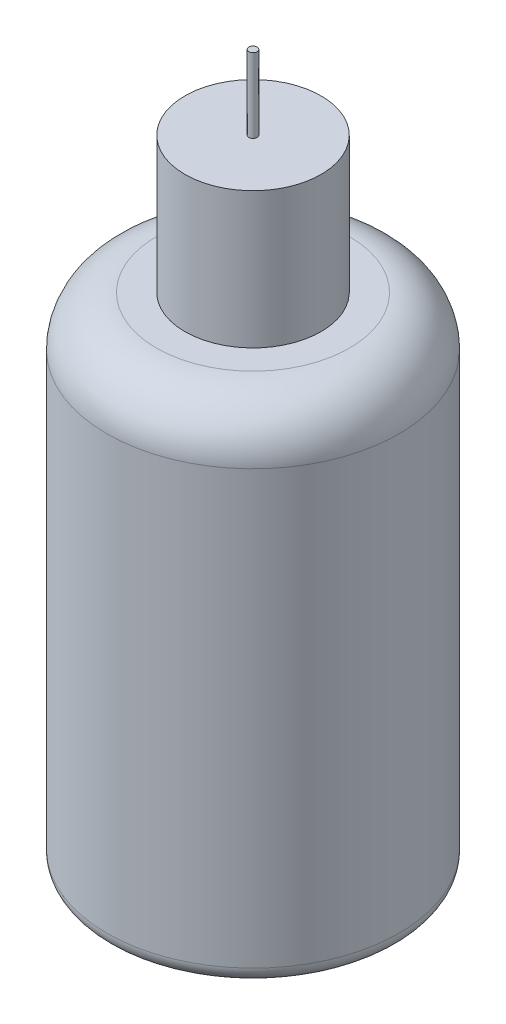
SolidWorks part; units mm, degrees
ref_plane "Alzado" through (0, 0, 0) normal (0, 0, 1) x (1, 0, 0)
ref_plane "Planta" through (0, 0, 0) normal (0, 1, 0) x (1, 0, 0)
ref_plane "Vista lateral" through (0, 0, 0) normal (1, 0, 0) x (0, 0, -1)
sketch "Croquis1" plane through (0, 0, 0) normal (0, 1, 0) x (1, 0, 0)
  circle A0 centre (0, 0) radius 17.7
  dimension "D1" = 35.4
extrude "Saliente-Extruir1" add sketch "Croquis1" along normal blind 60.4
fillet "Redondeo1" radius 6 1 edges at (0, 60.4, 17.7)
fillet "Redondeo2" radius 2 1 edges at (0, 0, 17.7)
sketch "Croquis2" plane through (0, 60.4, 0) normal (0, 1, 0) x (1, 0, 0)
  circle A0 centre (0, 0) radius 8.25
  dimension "D1" = 16.5
extrude "Saliente-Extruir2" add sketch "Croquis2" along normal blind 16.5
sketch "Croquis3" plane through (0, 76.9, 0) normal (0, 1, 0) x (1, 0, 0)
  circle A0 centre (0, 0) radius 0.5
  dimension "D1" = 1
extrude "Saliente-Extruir3" add sketch "Croquis3" along normal blind 9
